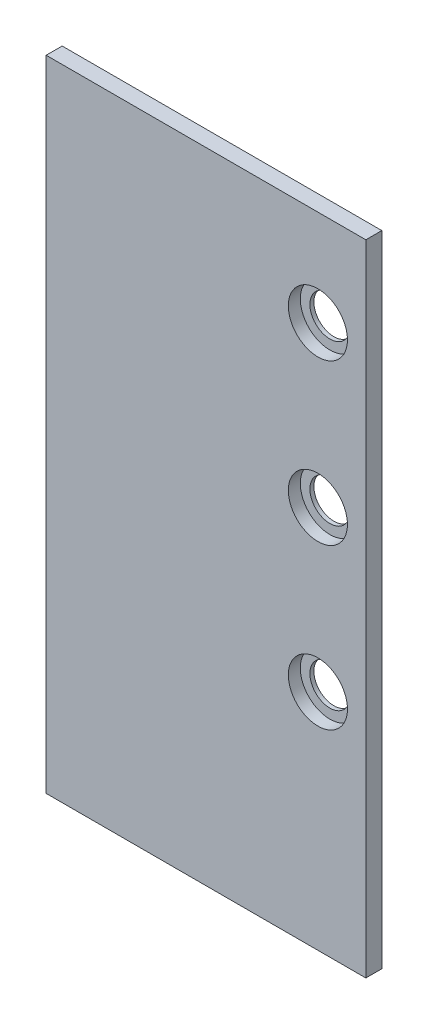
SolidWorks part; units mm, degrees
ref_plane "Front Plane" through (0, 0, 0) normal (0, 0, 1) x (1, 0, 0)
ref_plane "Top Plane" through (0, 0, 0) normal (0, 1, 0) x (1, 0, 0)
ref_plane "Right Plane" through (0, 0, 0) normal (1, 0, 0) x (0, 0, -1)
sketch "Sketch3" plane through (65.5497, 163.8664, 0) normal (0, 0, 1) x (1, 0, 0)
  line L0 (19.05, -76.2) -> (0, -76.2)
  line L1 (19.05, 177.8) -> (19.05, -76.2)
  line L4 (19.05, 177.8) -> (-107.95, 177.8)
  line L5 (-107.95, 177.8) -> (-107.95, -76.2)
  line L6 (-107.95, -76.2) -> (0, -76.2)
  dimension "D3" = 254
  dimension "D4" = 127
extrude "Boss-Extrude1" add sketch "Sketch3" along normal mid plane 6.35
sketch "Sketch4" plane through (0, 0, 3.175) normal (0, 0, 1) x (1, 0, 0)
  line L0 (84.5997, 87.6664) -> (84.5997, 341.6664) construction
  line L1 (-42.4003, 87.6664) -> (84.5997, 87.6664) construction
  circle A0 centre (65.5497, 176.5664) radius 11.7475
  dimension "D1" = 23.495
  dimension "D2" = 19.05
  dimension "D3" = 88.9
extrude "Cut-Extrude1" cut sketch "Sketch4" against normal blind 4.7625
sketch "Sketch5" plane through (0, 0, -1.5875) normal (0, 0, 1) x (1, 0, 0)
  circle A0 centre (65.5497, 176.5664) radius 7.9375
  dimension "D1" = 15.875
extrude "Cut-Extrude2" cut sketch "Sketch5" against normal through all
pattern_linear "LPattern1" count 3 spacing 63.5 along (0, 1, 0) of "Cut-Extrude1", "Cut-Extrude2"
equation "\"D_Bearing\" = 7 / 8in"
equation "\"Tol_Bearing\" = 0.05in"
equation "\"BearingHole\" = \"D_Bearing\"+\"Tol_Bearing\""
equation "\"ShaftDistance\" = 2.5in"
equation "\"D3@LocalLPattern1\"=\"ShaftDistance\""
equation "\"D4@LocalLPattern2\"=\"ShaftDistance\""
equation "\"SpokeDistance\" = 1.75in"
equation "\"D3@LocalLPattern2\"=\"SpokeDistance\"/2"
equation "\"D3@LocalLPattern3\"=\"ShaftDistance\""
equation "\"NumShaft\" = 3"
equation "\"D1@LocalLPattern1\"=\"NumShaft\""
equation "\"D2@LocalLPattern2\"=\"NumShaft\""
equation "\"D1@LocalLPattern3\"=\"NumShaft\""
equation "\"IntakeOpening\" = \"SpokeDistance\"+1.75in"
equation "\"SpokeLength\" = 2in"
equation "\"D1@Sketch4\"=\"BearingHole\""
equation "\"D3@Sketch4\"=\"IntakeOpening\""
equation "\"D3@LPattern1\"=\"ShaftDistance\""
equation "\"D1@LPattern1\"=\"NumShaft\""
